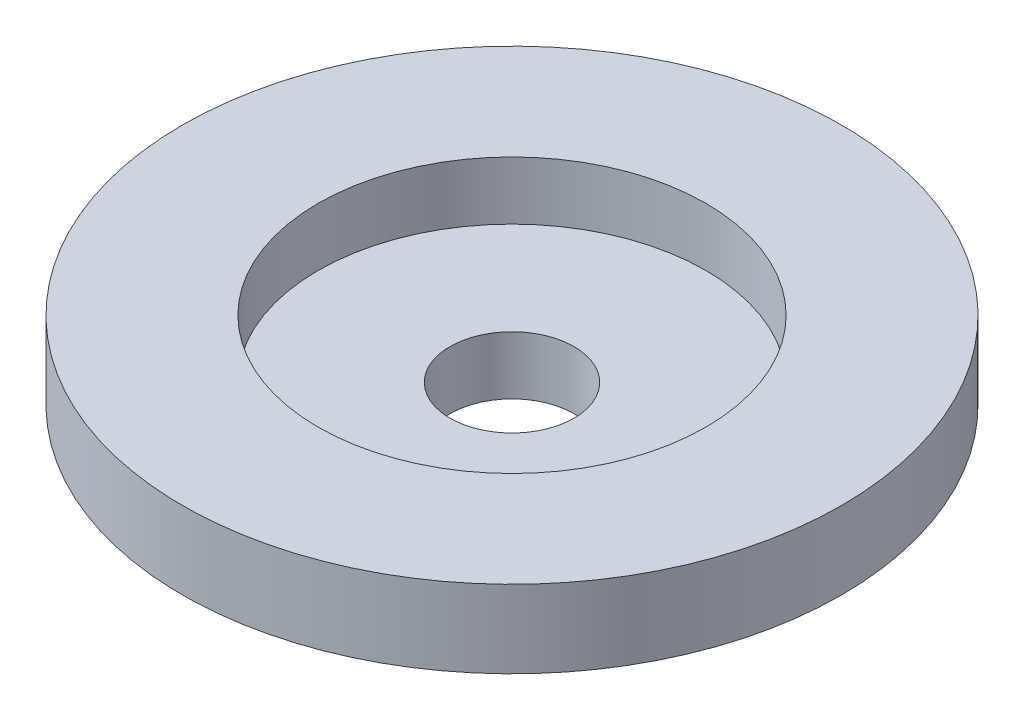
SolidWorks part; units mm, degrees
ref_plane "Front Plane" through (0, 0, 0) normal (0, 0, 1) x (1, 0, 0)
ref_plane "Top Plane" through (0, 0, 0) normal (0, 1, 0) x (1, 0, 0)
ref_plane "Right Plane" through (0, 0, 0) normal (1, 0, 0) x (0, 0, -1)
sketch "Sketch1" plane through (0, 0, 0) normal (0, 0, 1) x (1, 0, 0)
  line L0 (-1.6, 0) -> (-6.5, 0)
  line L1 (-6.5, 0) -> (-6.5, 1)
  line L2 (-6.5, 1) -> (-8.5, 1)
  line L3 (-8.5, 1) -> (-8.5, 3)
  line L4 (-8.5, 3) -> (-5, 3)
  line L5 (-5, 3) -> (-5, 1.5)
  line L6 (-5, 1.5) -> (-1.6, 1.5)
  line L7 (-1.6, 1.5) -> (-1.6, 0)
  line L8 (0, -1000) -> (0, 49000) construction
  dimension "D1" = 1.6
  dimension "D2" = 6.5
  dimension "D3" = 2
  dimension "D4" = 3.5
  dimension "D5" = 1
  dimension "D6" = 2
  dimension "D7" = 1.5
revolve "Revolve1" add sketch "Sketch1" angle 360 about L8
